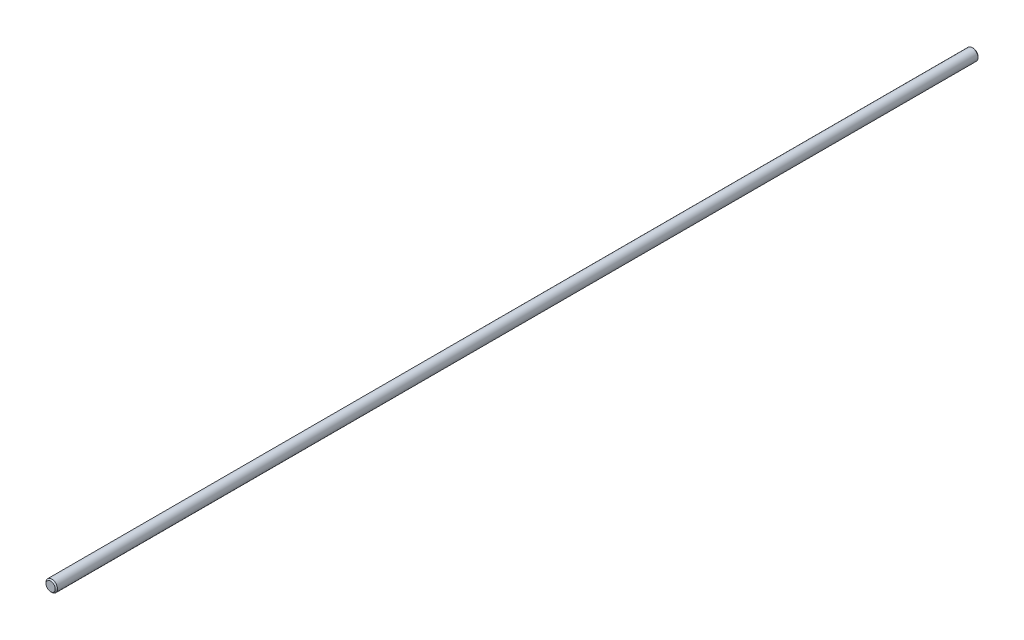
SolidWorks part; units mm, degrees
ref_plane "Front" through (0, 0, 0) normal (0, 0, 1) x (1, 0, 0)
ref_plane "Top" through (0, 0, 0) normal (0, 1, 0) x (1, 0, 0)
ref_plane "Right" through (0, 0, 0) normal (1, 0, 0) x (0, 0, -1)
sketch "Sketch1" plane through (0, 0, 0) normal (0, 0, 1) x (1, 0, 0)
  circle A0 centre (0, 0) radius 2.5
  dimension "D1" = 5
extrude "Extrude1" add sketch "Sketch1" along normal mid plane 400
chamfer "Chamfer1" distance 0.5 angle 45 2 edges at (2.5, 0, -200) (2.5, 0, 200)
equation "\"D1@Chamfer1\" = \"D1@Sketch1\" * .1"
